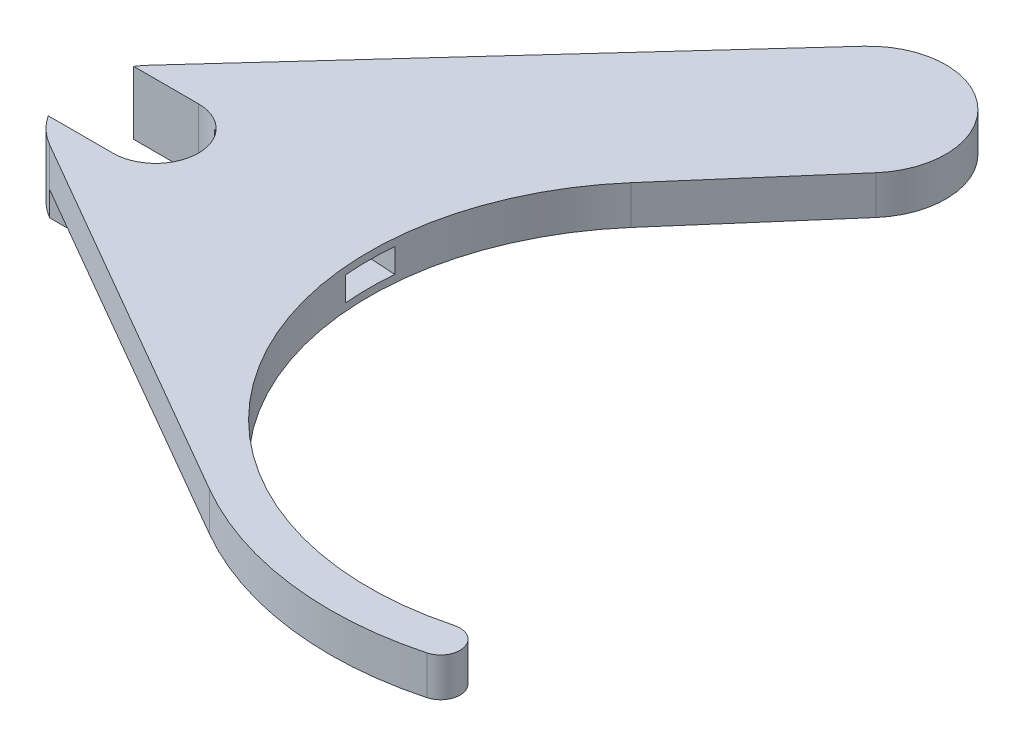
SolidWorks part; units mm, degrees
ref_plane "Front Plane" through (0, 0, 0) normal (0, 0, 1) x (1, 0, 0)
ref_plane "Top Plane" through (0, 0, 0) normal (0, 1, 0) x (1, 0, 0)
ref_plane "Right Plane" through (0, 0, 0) normal (1, 0, 0) x (0, 0, -1)
sketch "Sketch1" plane through (0, 0, 0) normal (0, 1, 0) x (1, 0, 0)
  line L0 (0, 0) -> (27.8118, 30.498) construction
  line L1 (0, 0) -> (41.275, 0) construction
  line L2 (23.296, 15.6137) -> (32.6062, 26.3344)
  line L3 (-4.692, 4.2787) -> (23.1198, 34.7768)
  line L4 (-3.175, -5.4993) -> (27.7812, -23.3719)
  line L5 (41.275, -23.8125) -> (41.275, -26.9875) construction
  line L6 (47.849, -24.5345) -> (47.4381, -23.0011) construction
  line L7 (47.849, -24.5345) -> (48.2599, -26.0679) construction
  circle A4 centre (41.275, 0) radius 19.05 construction
  circle A5 centre (41.275, 0) radius 23.8125
  circle A6 centre (41.275, 0) radius 26.9875
  circle A7 centre (27.8118, 30.498) radius 6.35
  arc A8 (41.275, -26.9875) -> (41.275, -23.8125) centre (41.275, -25.4) ccw construction
  circle A10 centre (0, 0) radius 6.35
  arc A11 (48.2599, -26.0679) -> (47.4381, -23.0011) centre (47.849, -24.5345) ccw
  dimension "D1" = 38.1
  dimension "D4" = 12.7
  dimension "D5" = 3.175
  dimension "D3" = 12.7
  dimension "D6" = 41.275
  dimension "D7" = 15
  dimension "D2" = 4.7625
extrude "Boss-Extrude1" add sketch "Sketch1" along normal blind 4.7625
sketch "Sketch2" plane through (0, 4.7625, 0) normal (0, 1, 0) x (1, 0, 0)
  line L0 (0, 3.5) -> (-5.2983, 3.5)
  line L1 (0, -3.5) -> (-5.2983, -3.5)
  line L2 (1.8028, 3) -> (17.8028, 2)
  line L3 (17.8028, 2) -> (17.8028, -2)
  line L4 (17.8028, -2) -> (1.8028, -3)
  line L5 (1.8028, 3) -> (1.8028, -3) construction
  circle A0 centre (0, 0) radius 3.5
  arc A1 (-4.692, 4.2787) -> (-3.175, -5.4993) centre (0, 0) ccw construction
  arc A2 (-5.2983, 3.5) -> (-5.2983, -3.5) centre (0, 0) ccw
  point P12 (1.8028, 0)
  point P16 (17.8028, 0)
  dimension "D1" = 7
  dimension "D2" = 6
  dimension "D3" = 4
  dimension "D4" = 16
sketch "Sketch5" plane through (0, 0, 0) normal (0, -1, 0) x (1, 0, 0)
  line L0 (0, 3.5) -> (-5.2983, 3.5) construction
  line L1 (0, -3.5) -> (-5.2983, -3.5) construction
  line L2 (0, 3.5) -> (-5.2983, 3.5)
  line L3 (0, -3.5) -> (-5.2983, -3.5)
  circle A0 centre (0, 0) radius 3.5 construction
  circle A1 centre (0, 0) radius 3.5
  arc M1 (-3.175, 5.4993) -> (-4.692, -4.2787) centre (0, 0) ccw
extrude "Cut-Extrude2" cut sketch "Sketch5" against normal offset from surface (3.3712 mm away) 1.3912 contours A1 | A1 L2 L3 M1 up to face at (22.9306, 4.7625, 0.3962)
sketch "Sketch6" plane through (0, 3.3713, 0) normal (0, -1, 0) x (1, 0, 0)
  line L0 (17.8028, -2) -> (17.8028, 2) construction
  line L1 (1.8028, -3) -> (17.8028, -2) construction
  line L2 (17.8028, 2) -> (1.8028, 3) construction
  line L3 (17.8028, -2) -> (17.8028, 2)
  line L4 (1.8028, -3) -> (17.8028, -2)
  line L5 (17.8028, 2) -> (1.8028, 3)
  circle A0 centre (0, 0) radius 3.5 construction
  arc A1 (1.8028, -3) -> (1.8028, 3) centre (0, 0) ccw
extrude "Cut-Extrude3" cut sketch "Sketch6" along normal offset from surface (1.98 mm away) 1.3912 up to face at (14.8799, 0, 0.2432)
sketch "Sketch10" plane through (-3.175, 0, 5.4993) normal (-0.5, 0, 0.866) x (0.866, 0, 0.5)
  line L0 (12.368, 0) -> (15.0706, 0) construction
  line L1 (15.0706, 4.7625) -> (12.368, 4.7625) construction
  line L2 (11.9327, 0) -> (52.5832, 0) construction
  line L3 (52.5832, 4.7625) -> (11.9327, 4.7625) construction
  line L4 (2.6339, 0) -> (15.1867, 0) construction
  line L5 (15.1867, 4.7625) -> (2.6339, 4.7625) construction
  line L6 (2.6339, 0) -> (-6.2028, 0) construction
  line L7 (-6.2028, 4.7625) -> (2.6339, 4.7625) construction
  line L8 (-6.35, 3.3712) -> (-2.8385, 3.3712) construction
  line L9 (-2.8385, 3.3712) -> (-2.8385, 0) construction
  line L10 (-2.8385, 0) -> (0, 0) construction
  line L11 (0, 4.7625) -> (-6.35, 4.7625) construction
  line L12 (-6.3385, 0) -> (-6.2028, 0) construction
  line L13 (-6.3385, 0) -> (-6.3385, 3.3712) construction
  line L14 (0, 0) -> (35.7452, 0) construction
  line L15 (35.7452, 4.7625) -> (0, 4.7625) construction
  line L16 (35.7452, 0) -> (54.8282, 0) construction
  line L17 (54.8282, 4.7625) -> (35.7452, 4.7625) construction
  line L18 (52.5832, 0) -> (55.2932, 0) construction
  line L19 (55.2932, 4.7625) -> (52.5832, 4.7625) construction
  line L20 (12.368, 0) -> (15.0706, 0) construction
  line L21 (15.0706, 4.7625) -> (12.368, 4.7625) construction
  line L22 (11.9327, 0) -> (52.5832, 0) construction
  line L23 (52.5832, 4.7625) -> (11.9327, 4.7625) construction
  line L24 (2.6339, 0) -> (15.1867, 0) construction
  line L25 (15.1867, 4.7625) -> (2.6339, 4.7625) construction
  line L26 (2.6339, 0) -> (-6.2028, 0) construction
  line L27 (-6.2028, 4.7625) -> (2.6339, 4.7625) construction
  line L28 (-6.35, 3.3712) -> (-2.8385, 3.3712) construction
  line L29 (-2.8385, 3.3712) -> (-2.8385, 0) construction
  line L30 (-2.8385, 0) -> (0, 0) construction
  line L31 (0, 4.7625) -> (-6.35, 4.7625) construction
  line L32 (-6.3385, 0) -> (-6.2028, 0) construction
  line L33 (-6.3385, 0) -> (-6.3385, 3.3712) construction
  line L34 (0, 0) -> (35.7452, 0) construction
  line L35 (35.7452, 4.7625) -> (0, 4.7625) construction
  line L36 (35.7452, 0) -> (54.8282, 0) construction
  line L37 (54.8282, 4.7625) -> (35.7452, 4.7625) construction
  line L38 (52.5832, 0) -> (55.2932, 0) construction
  line L39 (55.2932, 4.7625) -> (52.5832, 4.7625) construction
  line L41 (-6.35, 4.7625) -> (55.2932, 4.7625)
  line L42 (-6.35, 4.7625) -> (-6.35, 0)
  line L43 (-6.35, 0) -> (55.2932, 0)
  line L44 (55.2932, 4.7625) -> (55.2932, 0)
  line L45 (-6.35, 3.9688) -> (55.2932, 3.9688)
  line L46 (-6.35, 3.9688) -> (-6.35, 0.7938)
  line L47 (-6.35, 0.7938) -> (55.2932, 0.7938)
  line L48 (55.2932, 3.9688) -> (55.2932, 0.7938)
  point P26 (-6.35, 2.3813)
  line M29 (0, 0) -> (35.7452, 0)
  line M30 (35.7452, 0) -> (35.7452, 4.7625)
  line M31 (35.7452, 4.7625) -> (0, 4.7625)
  line M32 (0, 4.7625) -> (0, 0)
  dimension "D1" = 3.175
  dimension "D2" = 1.5875
extrude "Cut-Extrude4" cut sketch "Sketch10" against normal through all contours L42 L45 L41 M32 | L45 M32 M30 M31 | L45 L44 L41 M30 | L47 L43 L44 M30 | L47 M32 M29 M30 | L47 L42 L43 M32
sketch "Sketch11" plane through (0, 3.3713, 0) normal (0, -1, 0) x (1, 0, 0)
  line L0 (-5.2983, 3.5) -> (0, 3.5) construction
  line L1 (-5.2983, -3.5) -> (0, -3.5) construction
  line L2 (-5.2983, 3.5) -> (0, 3.5)
  line L3 (-5.2983, -3.5) -> (0, -3.5)
  arc A0 (-5.2983, 3.5) -> (-5.2983, -3.5) centre (0, 0) ccw construction
  arc A1 (0, -3.5) -> (0, 3.5) centre (0, 0) ccw construction
  arc A2 (-5.2983, 3.5) -> (-5.2983, -3.5) centre (0, 0) ccw
  arc A3 (0, -3.5) -> (0, 3.5) centre (0, 0) ccw
extrude "Cut-Extrude5" cut sketch "Sketch11" against normal blind 2.54
sketch "Sketch12" plane through (0, 0.7938, 0) normal (0, -1, 0) x (1, 0, 0)
  line L0 (-3.175, 5.4993) -> (27.7812, 23.3719) construction
  line L1 (23.1198, -34.7768) -> (-4.692, -4.2787) construction
  line L2 (-5.2983, 3.5) -> (0, 3.5) construction
  line L3 (-5.2983, -3.5) -> (0, -3.5) construction
  line L4 (-3.175, 5.4993) -> (-3.1737, 5.5)
  line L5 (-3.5783, -5.5) -> (-4.692, -4.2787)
  line L6 (-5.2983, 3.5) -> (0, 3.5)
  line L7 (-5.2983, -3.5) -> (0, -3.5)
  line L8 (-3.5783, -5.5) -> (0, -5.5)
  line L9 (-3.1737, 5.5) -> (0, 5.5)
  line L10 (-5.2983, -5.5) -> (0, -5.5) construction
  line L11 (-5.2983, 5.5) -> (0, 5.5) construction
  arc A0 (-5.2983, -3.5) -> (-4.692, -4.2787) centre (0, 0) ccw construction
  arc A1 (-3.175, 5.4993) -> (-5.2983, 3.5) centre (0, 0) ccw construction
  arc A2 (0, -3.5) -> (0, 3.5) centre (0, 0) ccw construction
  arc A3 (-5.2983, -3.5) -> (-4.692, -4.2787) centre (0, 0) ccw
  arc A4 (-3.175, 5.4993) -> (-5.2983, 3.5) centre (0, 0) ccw
  arc A5 (0, -3.5) -> (0, 3.5) centre (0, 0) ccw
  arc A6 (0, -5.5) -> (0, 5.5) centre (0, 0) ccw
  point P16 (0, 0)
  dimension "D1" = 2
extrude "Boss-Extrude2" add sketch "Sketch12" along normal blind 2
